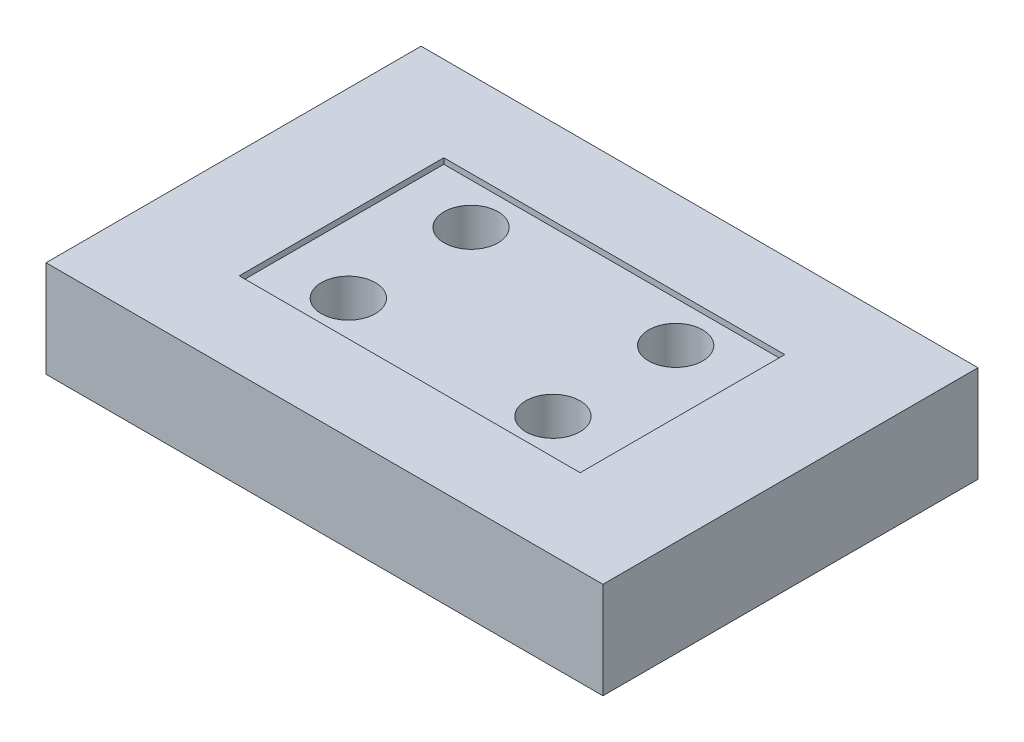
SolidWorks part; units mm, degrees
material "Polyurethane Foam Flexible"
ref_plane "Front Plane" through (0, 0, 0) normal (0, 0, 1) x (1, 0, 0)
ref_plane "Top Plane" through (0, 0, 0) normal (0, 1, 0) x (1, 0, 0)
ref_plane "Right Plane" through (0, 0, 0) normal (1, 0, 0) x (0, 0, -1)
sketch "Sketch1" plane through (0, 0, 0) normal (0, 1, 0) x (1, 0, 0)
  line L0 (-4587.7595, 0) -> (224800.2139, 0) construction
  line L1 (0, -4587.7595) -> (0, 224800.2139) construction
  line L3 (311.15, -209.55) -> (-311.15, -209.55)
  line L4 (311.15, -209.55) -> (311.15, 209.55)
  line L5 (311.15, 209.55) -> (-311.15, 209.55)
  line L6 (-311.15, -209.55) -> (-311.15, 209.55)
  line L7 (311.15, -209.55) -> (-311.15, 209.55) construction
  line L8 (311.15, 209.55) -> (-311.15, -209.55) construction
  point P4 (0, 0)
  dimension "D1" = 419.1
  dimension "D2" = 622.3
extrude "Boss-Extrude1" add sketch "Sketch1" along normal blind 107.95
fillet "Fillet1" [suppressed] radius 39.7002
sketch "Sketch2" [suppressed] plane through (0, 0, 0) normal (1, 0, 0) x (0, 0, -1)
  line L0 (-1000, 0) -> (49000, 0) construction
  line L1 (0, -1000) -> (0, 49000) construction
  line L5 (228.6, -11.1125) -> (279.4, 52.3875)
  line L10 (279.4, 39.6875) -> (279.4, 52.3875)
  arc A0 (228.6, -11.1125) -> (279.4, 39.6875) centre (228.6, 39.6875) ccw
  arc A1 (228.6, -11.1125) -> (279.4, 39.6875) centre (228.6, 39.6875) ccw
  point P17 (279.4, -11.1125)
  dimension "D3" = 50.8
  dimension "D4" = 63.5
extrude "Cut-Extrude1" [suppressed] cut sketch "Sketch2" against normal mid plane 2.54
pattern_linear "LPattern1" [suppressed] count 8 spacing 43.18 count 8 spacing 43.18
mirror "Mirror1" [suppressed] about plane through (0, 0, 0) normal (0, 0, 1)
sketch "Sketch3" plane through (0, 0, 0) normal (0, 0, 1) x (1, 0, 0)
  line L0 (-1000, 0) -> (49000, 0) construction
  line L1 (0, -1000) -> (0, 49000) construction
  line L2 (-376.5515, 166.0017) -> (-376.5515, 51.7017) construction
  line L3 (311.15, 107.95) -> (-311.15, 107.95) construction
  line L5 (-325.7515, -11.7983) -> (-376.5515, 51.7017)
  line L7 (0, 107.95) -> (0, -11.7983)
  line L8 (0, -11.7983) -> (-325.7515, -11.7983) construction
  line L9 (-376.5515, 51.7017) -> (-376.5515, 39.0017)
  line L10 (-376.5515, 39.0017) -> (-376.5515, 51.7017)
  arc A0 (-325.7515, -11.7983) -> (-376.5515, 39.0017) centre (-325.7515, 39.0017) cw
  arc A1 (-325.7515, -11.7983) -> (-376.5515, 39.0017) centre (-325.7515, 39.0017) cw
  point P17 (-376.5515, -11.7983)
  dimension "D3" = 50.8
  dimension "D1" = 381
  dimension "D2" = 177.8
  dimension "D4" = 63.5
extrude "Cut-Extrude2" [suppressed] cut sketch "Sketch3" against normal mid plane 2.54 contours A0 L5 L9
pattern_linear "LPattern2" [suppressed] count 5 spacing 44.45 count 5 spacing 44.45
mirror "Mirror2" [suppressed] about plane through (0, 0, 0) normal (1, 0, 0)
sketch "Sketch4" plane through (0, 107.95, 0) normal (0, 1, 0) x (1, 0, 0)
  line L0 (-1000, 0) -> (49000, 0) construction
  line L1 (0, -1000) -> (0, 49000) construction
  line L2 (-190.5, 0) -> (-190.5, 114.3) construction
  line L3 (0, -114.3) -> (-190.5, -114.3) construction
  line L4 (190.5, -114.3) -> (190.5, 0) construction
  line L5 (190.5, 114.3) -> (0, 114.3) construction
  line L6 (-190.5, -114.3) -> (-190.5, 0) construction
  line L7 (0, 114.3) -> (-190.5, 114.3) construction
  line L8 (190.5, 0) -> (190.5, 114.3) construction
  line L9 (190.5, -114.3) -> (0, -114.3) construction
  circle A0 centre (-114.3, 68.58) radius 30.1625
  circle A1 centre (-114.3, -68.58) radius 30.1625
  circle A2 centre (114.3, 68.58) radius 30.1625
  circle A3 centre (114.3, -68.58) radius 30.1625
  point P4 (0, 0)
  point P14 (-114.3, 68.58)
  dimension "D5" = 60.325
  dimension "D1" = 228.6
  dimension "D2" = 381
  dimension "D3" = 114.3
  dimension "D4" = 68.58
extrude "Cut-Extrude3" cut sketch "Sketch4" against normal through all
sketch "Sketch5" plane through (0, 107.95, 0) normal (0, 1, 0) x (1, 0, 0)
  line L0 (-1000, 0) -> (49000, 0) construction
  line L1 (0, -1000) -> (0, 49000) construction
  line L3 (190.5, -114.3) -> (-190.5, -114.3)
  line L4 (190.5, -114.3) -> (190.5, 114.3)
  line L5 (190.5, 114.3) -> (-190.5, 114.3)
  line L6 (-190.5, -114.3) -> (-190.5, 114.3)
  line L7 (190.5, -114.3) -> (-190.5, 114.3) construction
  line L8 (190.5, 114.3) -> (-190.5, -114.3) construction
  point P4 (0, 0)
  dimension "D1" = 381
  dimension "D2" = 228.6
extrude "Cut-Extrude4" cut sketch "Sketch5" against normal blind 6.35
